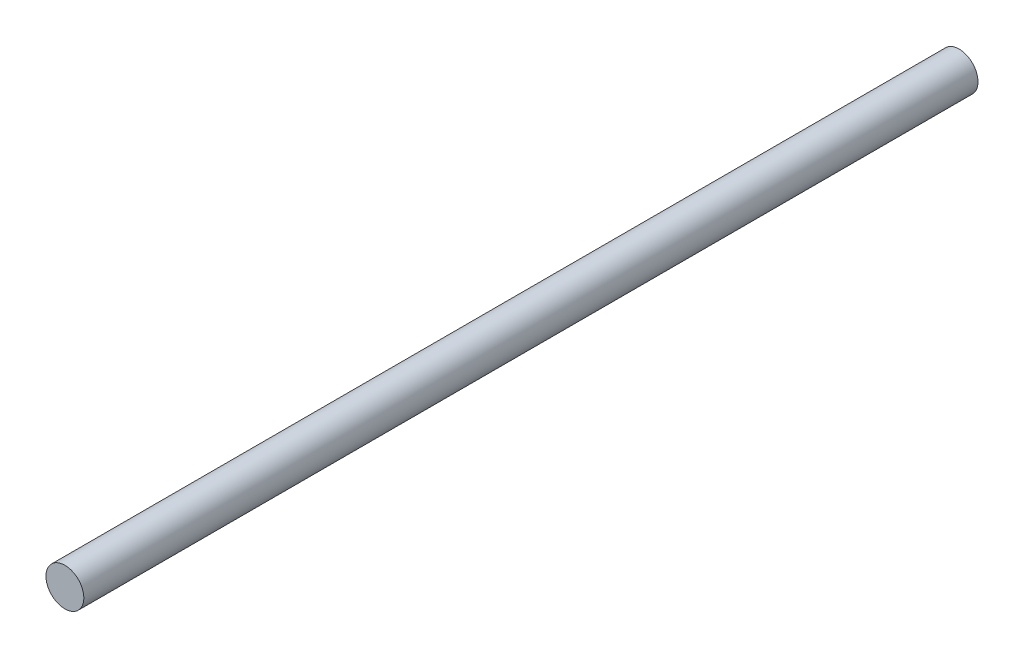
SolidWorks part; units mm, degrees
ref_plane "Alzado" through (0, 0, 0) normal (0, 0, 1) x (1, 0, 0)
ref_plane "Planta" through (0, 0, 0) normal (0, 1, 0) x (1, 0, 0)
ref_plane "Vista lateral" through (0, 0, 0) normal (1, 0, 0) x (0, 0, -1)
sketch "Croquis1" plane through (0, 0, 0) normal (0, 0, 1) x (1, 0, 0)
  circle A0 centre (0, 0) radius 6.35
  dimension "D1" = 12.7
sketch "Croquis2" plane through (0, 0, 0) normal (1, 0, 0) x (0, 0, -1)
  line L0 (0, 0) -> (300, 0)
  dimension "D1" = 300
sweep "Barrer1" add profiles "Croquis1" path "Croquis2"
